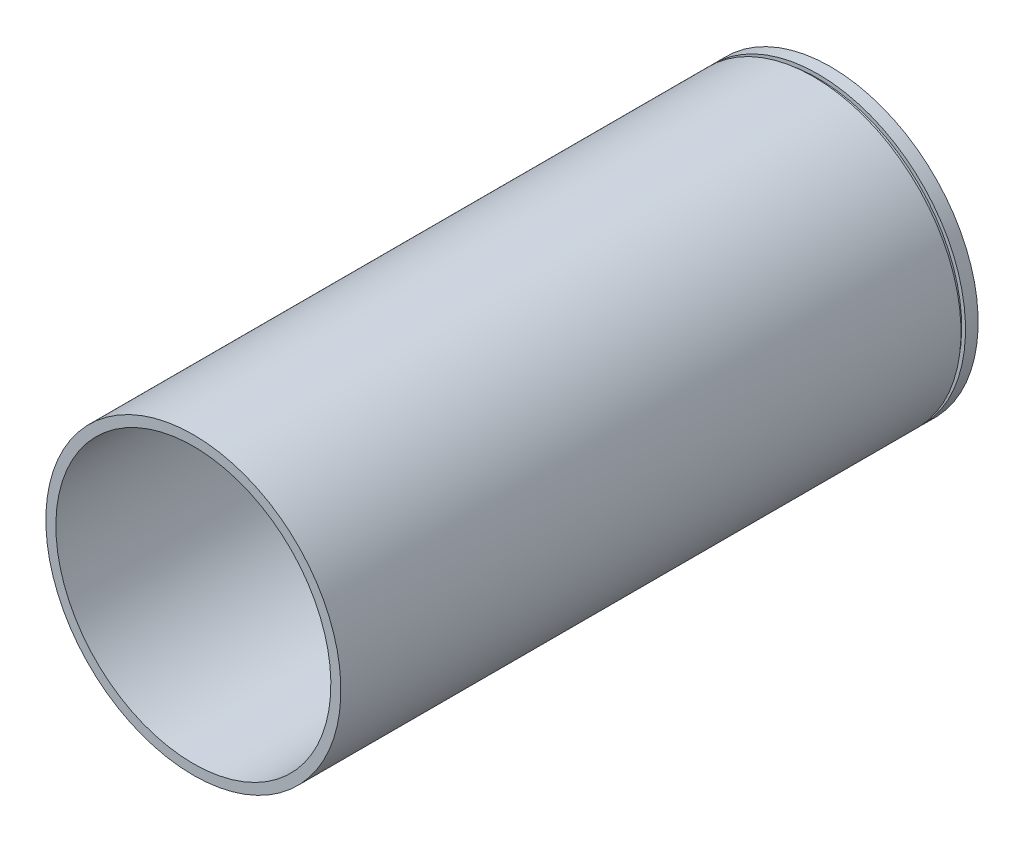
SolidWorks part; units mm, degrees
ref_plane "Front Plane" through (0, 0, 0) normal (0, 0, 1) x (1, 0, 0)
ref_plane "Top Plane" through (0, 0, 0) normal (0, 1, 0) x (1, 0, 0)
ref_plane "Right Plane" through (0, 0, 0) normal (1, 0, 0) x (0, 0, -1)
sketch "Sketch1" plane through (0, 0, 0) normal (1, 0, 0) x (0, 0, -1)
  line L0 (-63.9296, 0) -> (63.9296, 0) construction
  line L1 (283.3115, 136.57) -> (295, 136.57)
  line L2 (-295, 136.57) -> (279.1147, 136.57)
  line L3 (-295, 136.57) -> (-295, 127.3)
  line L4 (-295, 127.3) -> (295, 127.3)
  line L5 (295, 136.57) -> (295, 127.3)
  line L7 (279.1147, 136.57) -> (279.1147, 133.0491)
  line L8 (279.1147, 133.0491) -> (283.3115, 133.0491)
  line L9 (283.3115, 136.57) -> (283.3115, 133.0491)
  point P3 (0, 0)
  dimension "D1" = 127.3
  dimension "D2" = 9.27
  dimension "D3" = 590
revolve "Revolve2" add sketch "Sketch1" angle 360 about L0
